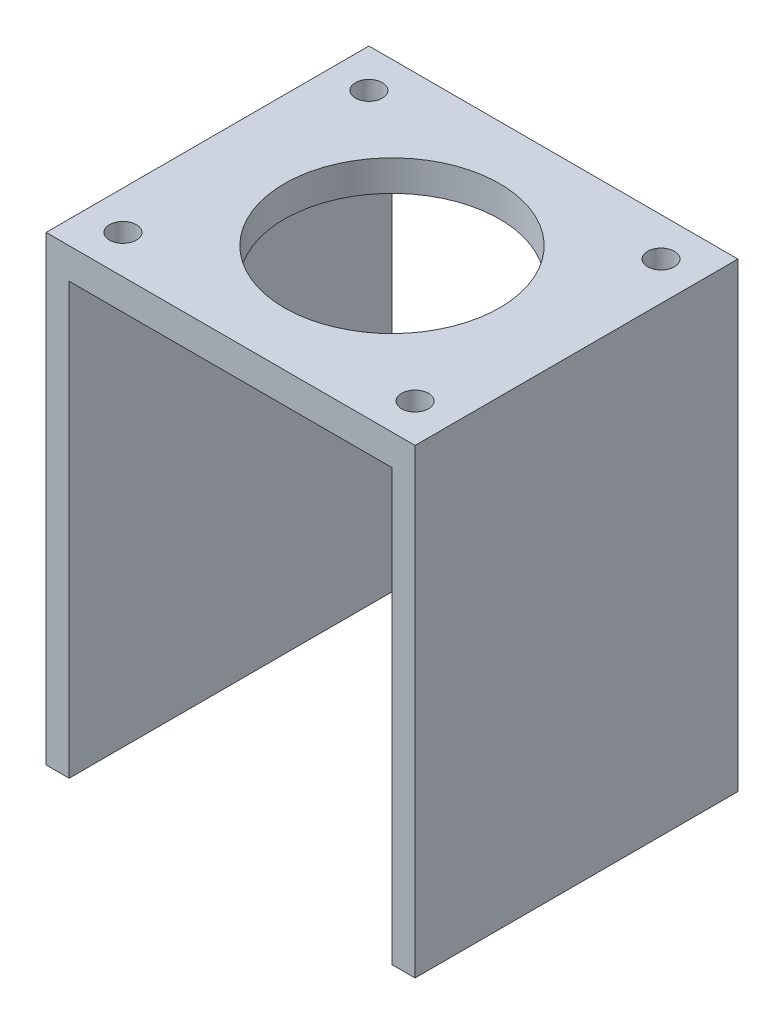
SolidWorks part; units mm, degrees
ref_plane "Front Plane" through (0, 0, 0) normal (0, 0, 1) x (1, 0, 0)
ref_plane "Top Plane" through (0, 0, 0) normal (0, 1, 0) x (1, 0, 0)
ref_plane "Right Plane" through (0, 0, 0) normal (1, 0, 0) x (0, 0, -1)
sketch "Sketch1" plane through (0, 0, 0) normal (0, 0, 1) x (1, 0, 0)
  line L0 (-21, -30) -> (-21, 26)
  line L1 (-24, -30) -> (-21, -30)
  line L2 (-24, -30) -> (-24, 30)
  line L3 (-24, 30) -> (24, 30)
  line L4 (24, -30) -> (24, 30)
  line L5 (-24, -30) -> (24, 30) construction
  line L6 (-24, 30) -> (24, -30) construction
  line L7 (-21, 26) -> (21, 26)
  line L8 (21, 26) -> (21, -30)
  line L9 (21, -30) -> (24, -30)
  point P0 (0, 0)
  dimension "D1" = 60
  dimension "D2" = 3
  dimension "D3" = 42
  dimension "D4" = 4
extrude "Boss-Extrude1" add sketch "Sketch1" along normal blind 42
sketch "Sketch2" plane through (0, 30, 0) normal (0, 1, 0) x (1, 0, 0)
  line L0 (24, -42) -> (-24, -42) construction
  line L1 (0, 0) -> (0, -42) construction
  line L2 (24, -42) -> (24, 0) construction
  line L3 (0, -21) -> (24, -21) construction
  circle A0 centre (19, -37) radius 1.75
  circle A1 centre (19, -5) radius 1.75
  circle A2 centre (-19, -37) radius 1.75
  circle A3 centre (-19, -5) radius 1.75
  circle A4 centre (0, -21) radius 14
  dimension "D2" = 3.5
  dimension "D4" = 28
  dimension "D1" = 5
  dimension "D3" = 5
extrude "Cut-Extrude1" cut sketch "Sketch2" against normal through all
